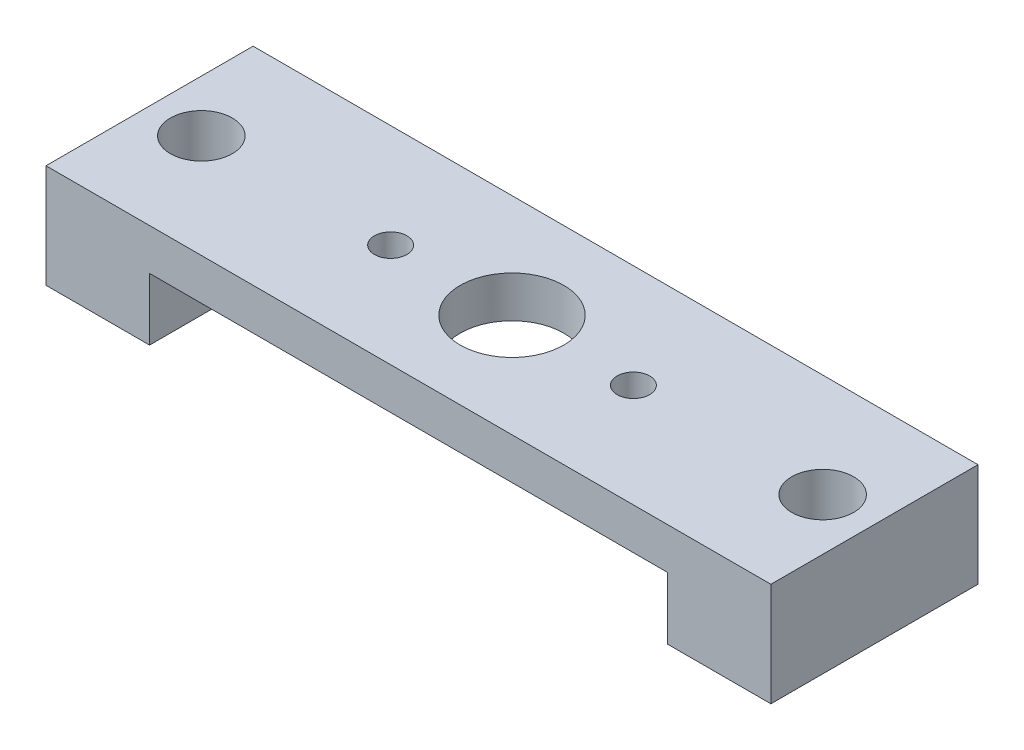
SolidWorks part; units mm, degrees
ref_plane "Front Plane" through (0, 0, 0) normal (0, 0, 1) x (1, 0, 0)
ref_plane "Top Plane" through (0, 0, 0) normal (0, 1, 0) x (1, 0, 0)
ref_plane "Right Plane" through (0, 0, 0) normal (1, 0, 0) x (0, 0, -1)
sketch "Sketch1" plane through (0, 0, 0) normal (0, 1, 0) x (1, 0, 0)
  line L1 (0, 0) -> (44.45, 0)
  line L2 (0, 0) -> (0, 12.7)
  line L3 (0, 12.7) -> (44.45, 12.7)
  line L4 (44.45, 0) -> (44.45, 12.7)
  dimension "D1" = 12.7
  dimension "D2" = 44.45
extrude "Boss-Extrude1" add sketch "Sketch1" along normal blind 2.54
sketch "Sketch2" plane through (0, 0, 0) normal (0, -1, 0) x (1, 0, 0)
  line L0 (44.45, -12.7) -> (0, -12.7) construction
  line L1 (0, 0) -> (6.35, 0)
  line L2 (0, 0) -> (0, -12.7)
  line L3 (0, -12.7) -> (6.35, -12.7)
  line L4 (6.35, 0) -> (6.35, -12.7)
  line L6 (44.45, 0) -> (38.1, 0)
  line L7 (44.45, 0) -> (44.45, -12.7)
  line L8 (44.45, -12.7) -> (38.1, -12.7)
  line L9 (38.1, 0) -> (38.1, -12.7)
  dimension "D1" = 6.35
extrude "Boss-Extrude2" add sketch "Sketch2" along normal blind 3.81
hole_wizard "#6 Clearance Hole1" positions "Sketch6" profile "Sketch5" hole size "#6" standard "ANSI Inch" end condition through all
sketch "Sketch6" plane through (0, 2.54, 0) normal (0, 1, 0) x (1, 0, 0)
  line L0 (0, 6.35) -> (44.45, 6.35) construction
  line L2 (44.45, 0) -> (44.45, 12.7) construction
  line L4 (0, 12.7) -> (0, 0) construction
  point P0 (3.175, 6.35)
  point P2 (41.275, 6.35)
  point P13 (0, 6.35)
  point P16 (0, 0)
  point P17 (0, 0)
  dimension "D1" = 3.175
  dimension "D2" = 3.175
sketch "Sketch5" plane through (3.175, 2.54, -6.35) normal (1, 0, 0) x (0, 0, 1)
  line L0 (0, 0) -> (0, 6.35)
  line L1 (0, 6.35) -> (1.8986, 6.35)
  line L2 (1.8986, 6.35) -> (1.8986, 0)
  line L5 (1.8986, 0) -> (0, 0)
  line L11 (0, -6.35) -> (0, 107.95) construction
  dimension "Thru Hole Dia." = 3.7973
  dimension "Thru Hole Depth" = 6.35
hole_wizard "#3-48 Tapped Hole1" positions "Sketch7" profile "Sketch8" tap size "#3-48" standard "ANSI Inch" end condition through all
sketch "Sketch7" plane through (0, 2.54, 0) normal (0, 1, 0) x (1, 0, 0)
  line L0 (0, 6.35) -> (44.45, 6.35) construction
  line L1 (0, 12.7) -> (0, 0) construction
  line L2 (44.45, 0) -> (44.45, 12.7) construction
  line L3 (14.7828, 6.35) -> (29.6672, 6.35) construction
  point P0 (14.7828, 6.35)
  point P2 (29.6672, 6.35)
  point P18 (22.225, 6.35)
  point P19 (22.225, 6.35)
  point P20 (0, 0)
  dimension "D1" = 14.8844
sketch "Sketch8" plane through (14.7828, 2.54, -6.35) normal (1, 0, 0) x (0, 0, 1)
  line L0 (0, 0) -> (0, 6.35)
  line L1 (0, 6.35) -> (0.9969, 6.35)
  line L2 (0.9969, 6.35) -> (0.9969, 0)
  line L5 (0.9969, 0) -> (0, 0)
  line L11 (0, -6.35) -> (0, 107.95) construction
  dimension "Thru Tap Drill Dia." = 1.9939
  dimension "Thru Tap Drill Depth" = 6.35
cosmetic thread "Hole Thread1" parameters "D2"=2.5146
cosmetic thread "Hole Thread2" parameters "D2"=2.5146
hole_wizard "1/4 (0.25) Diameter Hole1" positions "Sketch9" profile "Sketch10" hole size "1/4" standard "ANSI Inch" end condition through all
sketch "Sketch9" plane through (0, 2.54, 0) normal (0, 1, 0) x (1, 0, 0)
  line L0 (0, 6.35) -> (44.45, 6.35) construction
  line L1 (0, 12.7) -> (0, 0) construction
  line L2 (44.45, 0) -> (44.45, 12.7) construction
  line L4 (22.225, 12.7) -> (22.225, 0) construction
  line L5 (44.45, 12.7) -> (0, 12.7) construction
  line L6 (0, 0) -> (44.45, 0) construction
  point P0 (22.225, 6.35)
  point P19 (0, 0)
  point P20 (22.225, 6.35)
sketch "Sketch10" plane through (22.225, 2.54, -6.35) normal (1, 0, 0) x (0, 0, 1)
  line L0 (0, 0) -> (0, 6.35)
  line L1 (0, 6.35) -> (3.175, 6.35)
  line L2 (3.175, 6.35) -> (3.175, 0)
  line L5 (3.175, 0) -> (0, 0)
  line L11 (0, -6.35) -> (0, 107.95) construction
  dimension "Thru Hole Dia." = 6.35
  dimension "Thru Hole Depth" = 6.35
